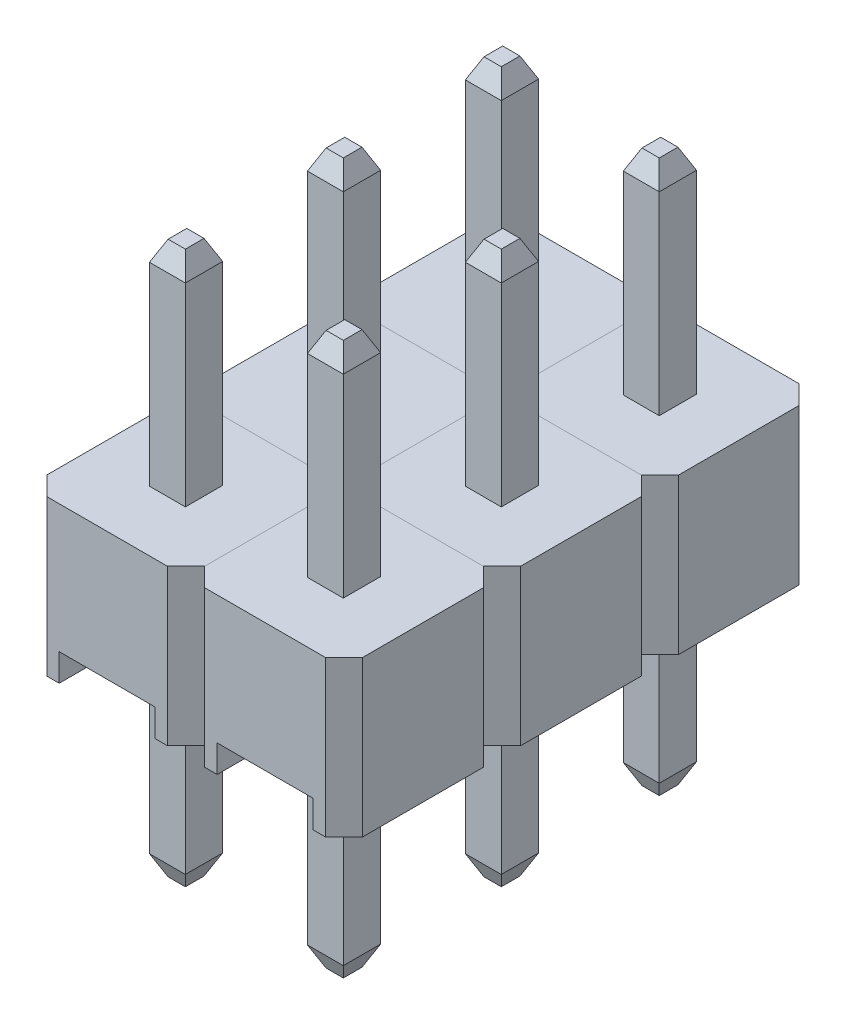
SolidWorks part; units mm, degrees
material "Latón"
ref_plane "Alzado" through (0, 0, 0) normal (0, 0, 1) x (1, 0, 0)
ref_plane "Planta" through (0, 0, 0) normal (0, 1, 0) x (1, 0, 0)
ref_plane "Vista lateral" through (0, 0, 0) normal (1, 0, 0) x (0, 0, -1)
sketch "Croquis1" plane through (0, 0, 0) normal (0, 1, 0) x (1, 0, 0)
  line L0 (0.3, 0) -> (2.24, 0)
  line L1 (2.54, 0.3) -> (2.54, 2.24)
  line L2 (2.24, 2.54) -> (0.3, 2.54)
  line L3 (0, 2.24) -> (0, 0.3)
  line L4 (0.3, 2.54) -> (0, 2.24)
  line L5 (2.54, 2.24) -> (2.24, 2.54)
  line L6 (2.24, 0) -> (2.54, 0.3)
  line L7 (0, 0.3) -> (0.3, 0)
  point P0 (0, 0)
  point P1 (2.54, 0)
  point P2 (0, 2.54)
  point P3 (2.54, 2.54)
  dimension "D1" = 0.3
  dimension "D2" = 45
  dimension "D3" = 0.3
  dimension "D4" = 45
  dimension "D5" = 0.3
  dimension "D6" = 45
  dimension "D7" = 0.3
  dimension "D8" = 45
extrude "Cuerpo Plástico" add sketch "Croquis1" along normal blind 2.5
sketch "Croquis2" plane through (0, 0, 0) normal (0, -1, 0) x (1, 0, 0)
  line L0 (0.5, 0) -> (0.5, -2.54)
  line L3 (0, -2.24) -> (0, -0.3) construction
  line L4 (2.04, 0) -> (2.04, -2.54)
  line L7 (2.54, -0.3) -> (2.54, -2.24) construction
  line L8 (0.5, 0) -> (2.04, 0)
  line L9 (0.5, -2.54) -> (2.04, -2.54)
  dimension "D1" = 0.5
  dimension "D2" = 0.5
  dimension "D3" = 1.54
extrude "Ranura" cut sketch "Croquis2" against normal blind 0.44
sketch "Croquis3" plane through (0, 2.5, 0) normal (0, 1, 0) x (1, 0, 0)
  line L0 (0.9812, 1.57) -> (1.5588, 1.57)
  line L1 (1.27, 2.54) -> (1.27, 1.57) construction
  line L2 (2.24, 2.54) -> (0.3, 2.54) construction
  line L3 (1.5588, 1.57) -> (1.5588, 0.97)
  line L4 (1.5588, 0.97) -> (0.9812, 0.97)
  line L5 (0.9812, 0.97) -> (0.9812, 1.57)
  line L6 (0, 1.27) -> (0.9812, 1.27) construction
  line L7 (0, 2.24) -> (0, 0.3) construction
  dimension "D1" = 0.6
extrude "Pin" add sketch "Croquis3" along normal blind 3.44 and the other way blind 5.44
chamfer "Chaflán1" distance 0.15 angle 65 4 edges at (1.27, 5.94, -1.57) (1.5588, 5.94, -1.27) (1.27, 5.94, -0.97) (0.9812, 5.94, -1.27)
chamfer "Chaflán2" distance 0.15 angle 65 4 edges at (1.27, -2.94, -0.97) (1.5588, -2.94, -1.27) (1.27, -2.94, -1.57) (0.9812, -2.94, -1.27)
sketch "Dirección" plane through (0, 0, 0) normal (-1, 0, 0) x (0, 0, 1)
  line L0 (-2.24, 1.25) -> (-0.3, 1.25) construction
  line L1 (-2.24, 2.5) -> (-2.24, 0) construction
  line L2 (-0.3, 2.5) -> (-0.3, 0) construction
sketch "Dirección 2" plane through (0, 0, -2.54) normal (0, 0, -1) x (-1, 0, 0)
  line L0 (-2.24, 1.25) -> (-0.3, 1.25) construction
  line L1 (-2.24, 2.5) -> (-2.24, 0) construction
  line L2 (-0.3, 2.5) -> (-0.3, 0) construction
pattern_linear "Matriz" count 3 spacing 2.54 along (0, 0, 1) count 2 spacing 2.54 along (1, 0, 0) of bodies 103
other "PropertyManager"
